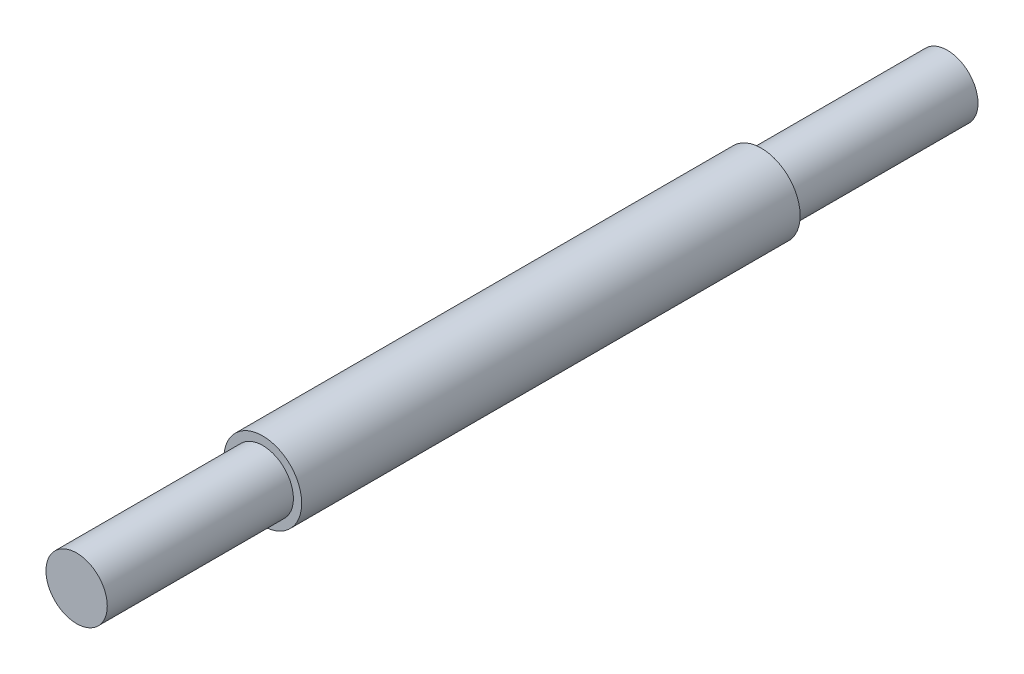
SolidWorks part; units mm, degrees
ref_plane "Front Plane" through (0, 0, 0) normal (0, 0, 1) x (1, 0, 0)
ref_plane "Top Plane" through (0, 0, 0) normal (0, 1, 0) x (1, 0, 0)
ref_plane "Right Plane" through (0, 0, 0) normal (1, 0, 0) x (0, 0, -1)
sketch "Sketch2" plane through (0, 0, 0) normal (0, 0, 1) x (1, 0, 0)
  circle A0 centre (0, 0) radius 2.5
  dimension "D1" = 5
extrude "Boss-Extrude1" add sketch "Sketch2" along normal blind 35.495 and the other way blind 35.495
sketch "Sketch3" plane through (0, 0, 0) normal (0, 0, 1) x (1, 0, 0)
  circle A0 centre (0, 0) radius 3.175
  dimension "D1" = 6.35
extrude "Boss-Extrude2" add sketch "Sketch3" along normal blind 20.32 and the other way blind 20.32
